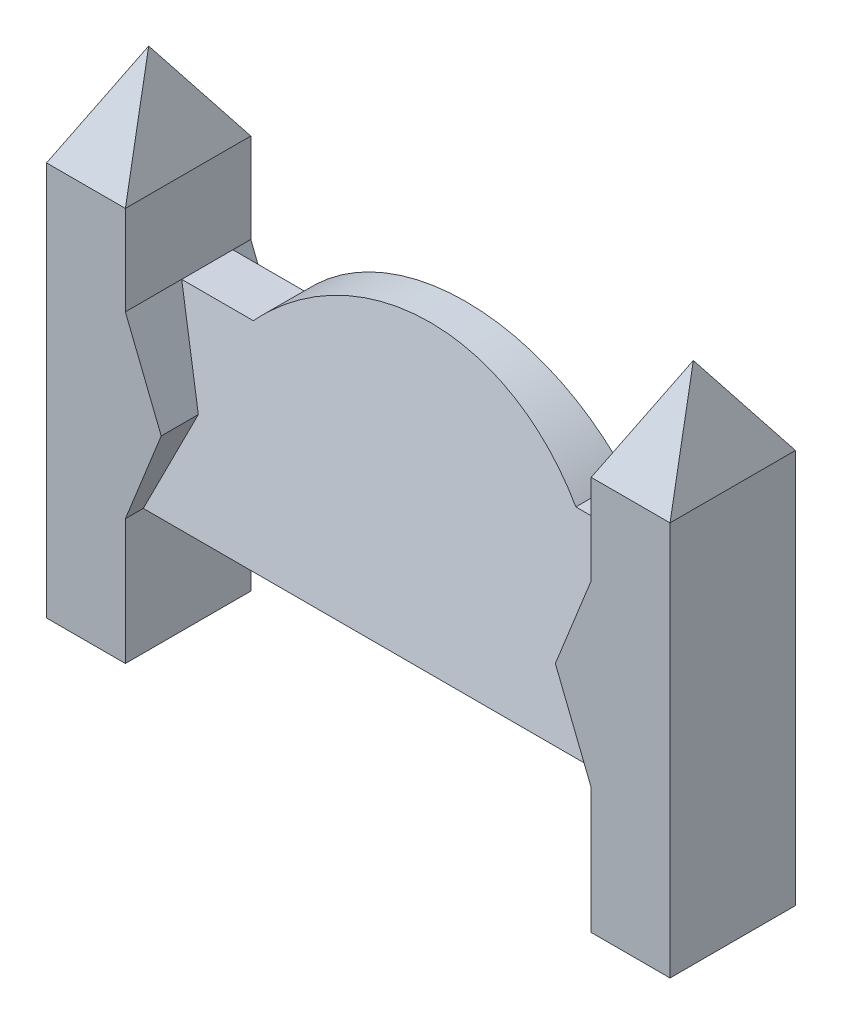
SolidWorks part; units mm, degrees
ref_plane "Front" through (0, 0, 0) normal (0, 0, 1) x (1, 0, 0)
ref_plane "Top" through (0, 0, 0) normal (0, 1, 0) x (1, 0, 0)
ref_plane "Right" through (0, 0, 0) normal (1, 0, 0) x (0, 0, -1)
sketch "Sketch1" plane through (0, 0, 0) normal (0, 0, 1) x (1, 0, 0)
  line L0 (220, 850) -> (220, 1100)
  line L1 (0, 0) -> (220, 0)
  line L2 (0, 0) -> (0, 1100)
  line L3 (0, 1100) -> (220, 1100)
  line L4 (220, 0) -> (220, 350)
  line L5 (1740, 0) -> (1520, 0)
  line L6 (870, 850) -> (870, 1100) construction
  line L7 (1520, 0) -> (1520, 350)
  line L8 (1420, 600) -> (1520, 350)
  line L9 (220, 850) -> (320, 600)
  line L10 (320, 600) -> (220, 350)
  line L11 (1520, 850) -> (1420, 600)
  line L12 (1740, 0) -> (1740, 1100)
  line L13 (1740, 1100) -> (1520, 1100)
  line L14 (1520, 850) -> (1520, 1100)
  dimension "D1" = 220
  dimension "D2" = 1100
extrude "Extrude1" add sketch "Sketch1" along normal blind 350
sketch "Sketch2" plane through (0, 0, 0) normal (-1, 0, 0) x (0, 0, 1)
  line L1 (50, 1050) -> (150, 1050)
  line L2 (50, 1050) -> (50, 350)
  line L3 (50, 350) -> (300, 350)
  line L4 (350, 1100) -> (350, 0) construction
  line L5 (0, 1100) -> (0, 0) construction
  line L7 (350, 0) -> (0, 0) construction
  line L8 (300, 350) -> (150, 1050)
  line L9 (350, 850) -> (0, 850) construction
  dimension "D1" = 200
  dimension "D2" = 50
  dimension "D3" = 50
  dimension "D4" = 350
  dimension "D5" = 100
extrude "Extrude2" add sketch "Sketch2" against normal blind 1300 from offset 220
sketch "Sketch3" plane through (0, 1100, 0) normal (0, 1, 0) x (-1, 0, 0)
  line L1 (0, 0) -> (-220, 0)
  line L2 (0, 0) -> (0, 350)
  line L3 (0, 350) -> (-220, 350)
  line L4 (-220, 0) -> (-220, 350)
ref_plane "Plane1" through (0, 0, 175) normal (0, 0, 1) x (1, 0, 0)
sketch "Sketch4" plane through (0, 1100, 0) normal (0, 1, 0) x (-1, 0, 0)
  line L1 (-1520, 0) -> (-1740, 0)
  line L2 (-1520, 0) -> (-1520, 350)
  line L3 (-1520, 350) -> (-1740, 350)
  line L4 (-1740, 0) -> (-1740, 350)
sketch "Sketch5" plane through (0, 0, 175) normal (0, 0, 1) x (1, 0, 0)
  line L0 (110, 1100) -> (110, 1171.886) construction
  line L1 (0, 1100) -> (220, 1100) construction
  point P4 (110, 1350)
  dimension "D1" = 250
loft "Loft1" add profiles "Sketch3", "Sketch5"
sketch "Sketch6" plane through (0, 0, 175) normal (0, 0, 1) x (1, 0, 0)
  line L0 (1630, 1100) -> (1630, 1150.762) construction
  line L1 (1520, 1100) -> (1740, 1100) construction
  point P4 (1630, 1350)
  dimension "D1" = 250
loft "Loft2" add profiles "Sketch6", "Sketch4"
sketch "Sketch7" plane through (0, 0, 0) normal (0, 0, 1) x (1, 0, 0)
  line L0 (870, 350) -> (870, 850) construction
  line L1 (1520, 350) -> (220, 350) construction
  line L2 (1520, 850) -> (1520, 1176.4332)
  line L3 (1520, 1176.4332) -> (220, 1176.4332)
  line L4 (1520, 1050) -> (220, 1050) construction
  line L5 (1520, 850) -> (1320, 850)
  line L6 (220, 850) -> (220, 1176.4332)
  line L7 (420, 850) -> (220, 850)
  line L8 (870, 1050) -> (870, 1439.9475) construction
  arc A0 (1320, 850) -> (420, 850) centre (870, 443.75) ccw
extrude "Cut-Extrude1" cut sketch "Sketch7" along normal through all
